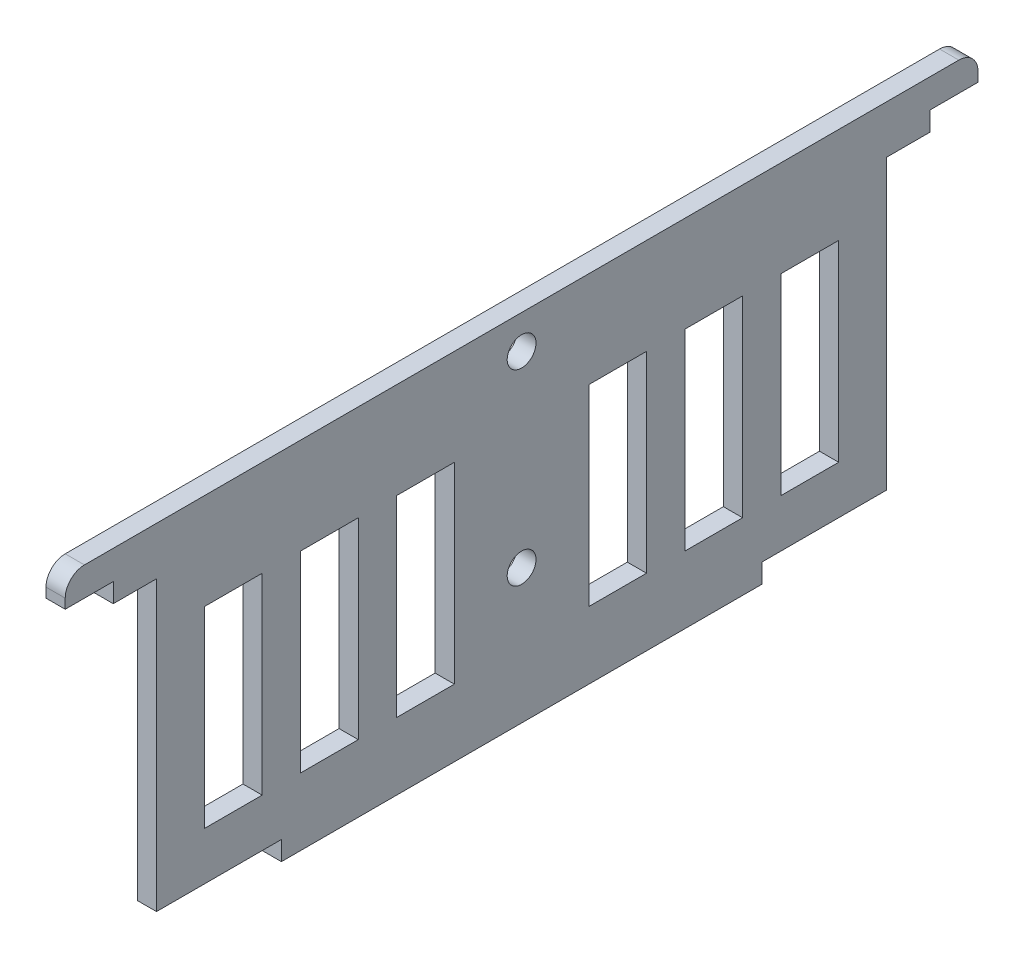
SolidWorks part; units mm, degrees
material "Acrylic (Medium-high impact)"
ref_plane "Front Plane" through (0, 0, 0) normal (0, 0, 1) x (1, 0, 0)
ref_plane "Top Plane" through (0, 0, 0) normal (0, 1, 0) x (1, 0, 0)
ref_plane "Right Plane" through (0, 0, 0) normal (1, 0, 0) x (0, 0, -1)
sketch "Sketch1" plane through (0, 0, 0) normal (1, 0, 0) x (0, 0, -1)
  line L0 (-25, -15) -> (-25, -17)
  line L2 (-38, 15) -> (-38, -15)
  line L3 (-38, -15) -> (-25, -15)
  line L4 (38, 15) -> (38, -15)
  line L5 (-38, 15) -> (38, -15) construction
  line L6 (-38, -15) -> (38, 15) construction
  line L7 (-25, -17) -> (25, -17)
  line L8 (25, -17) -> (25, -15)
  line L9 (25, -15) -> (38, -15)
  line L10 (38, 15) -> (42.5, 15)
  line L14 (-42.5, 15) -> (-38, 15)
  line L15 (-25, -15) -> (0, -15) construction
  line L16 (0, -15) -> (0, -3) construction
  line L17 (0, -3) -> (0, 16.5) construction
  line L18 (42.5, 15) -> (42.5, 17)
  line L19 (42.5, 17) -> (47.5, 17)
  line L20 (47.5, 17) -> (47.5, 20)
  line L21 (-47.5, 17) -> (-47.5, 20)
  line L22 (-42.5, 17) -> (-47.5, 17)
  line L23 (-42.5, 15) -> (-42.5, 17)
  line L24 (-47.5, 20) -> (47.5, 20)
  line L25 (0, 0) -> (10, 0) construction
  line L26 (10, 0) -> (20, 0) construction
  line L27 (20, 0) -> (30, 0) construction
  line L28 (17, 10) -> (23, 10)
  line L29 (27, 10) -> (33, 10)
  line L30 (27, 10) -> (27, -10)
  line L31 (27, -10) -> (33, -10)
  line L32 (33, 10) -> (33, -10)
  line L33 (27, 10) -> (33, -10) construction
  line L34 (27, -10) -> (33, 10) construction
  line L35 (23, 10) -> (23, -10)
  line L36 (17, 10) -> (17, -10)
  line L37 (17, -10) -> (23, -10)
  line L38 (7, 10) -> (13, 10)
  line L39 (13, 10) -> (13, -10)
  line L40 (7, 10) -> (7, -10)
  line L41 (7, -10) -> (13, -10)
  line L42 (-7, -10) -> (-13, -10)
  line L43 (-13, 10) -> (-13, -10)
  line L44 (-7, 10) -> (-7, -10)
  line L45 (-7, 10) -> (-13, 10)
  line L46 (-17, -10) -> (-23, -10)
  line L47 (-17, 10) -> (-17, -10)
  line L48 (-17, 10) -> (-23, 10)
  line L49 (-23, 10) -> (-23, -10)
  line L50 (-27, -10) -> (-33, -10)
  line L51 (-27, 10) -> (-27, -10)
  line L52 (-33, 10) -> (-33, -10)
  line L53 (-27, 10) -> (-33, 10)
  circle A0 centre (0, 16.5) radius 1.5
  circle A1 centre (0, -3) radius 1.5
  point P0 (0, 0)
  dimension "D9" = 3
  dimension "D10" = 3
  dimension "D15" = 20
  dimension "D1" = 30
  dimension "D2" = 76
  dimension "D3" = 2
  dimension "D4" = 50
  dimension "D5" = 10
  dimension "D6" = 4.5
  dimension "D7" = 12
  dimension "D8" = 19.5
  dimension "D11" = 2
  dimension "D12" = 5
  dimension "D13" = 10
  dimension "D14" = 10
  dimension "D16" = 6
  dimension "D17" = 3
extrude "Boss-Extrude1" add sketch "Sketch1" along normal blind 2
fillet "Fillet2" radius 2 2 edges at (1, 20, 47.5) (1, 20, -47.5)
